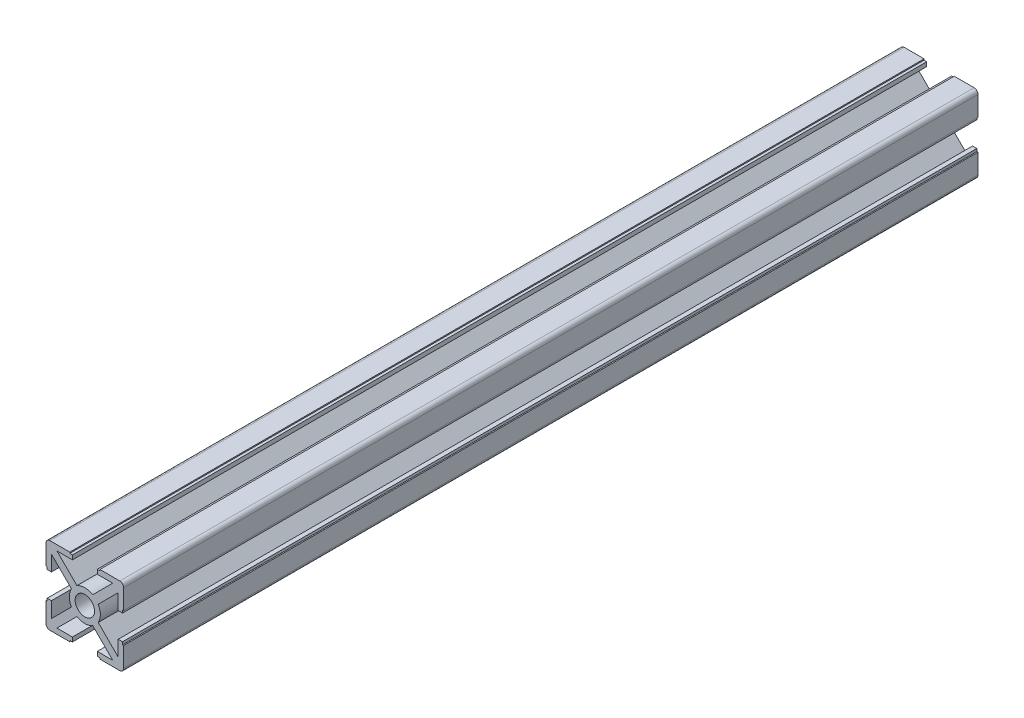
SolidWorks part; units mm, degrees
material "1060 Alloy"
ref_plane "Ön Düzlem" through (0, 0, 0) normal (0, 0, 1) x (1, 0, 0)
ref_plane "Üst Düzlem" through (0, 0, 0) normal (0, 1, 0) x (1, 0, 0)
ref_plane "Sağ Düzlem" through (0, 0, 0) normal (1, 0, 0) x (0, 0, -1)
sketch "Sketch1" plane through (0, 0, 0) normal (0, 0, 1) x (1, 0, 0)
  line L0 (-9.7071, -3.2) -> (-8.6, -3.2)
  line L2 (-10, -3.8775) -> (-10, -9)
  line L3 (-9, -10) -> (-3.8775, -10)
  line L5 (-10, -3.8775) -> (-9.7071, -3.8775)
  line L6 (-10, -10) -> (-9.7071, -9.7071) construction
  line L9 (-3.2, -8.6) -> (-7.1858, -8.6)
  line L10 (-8.6, -3.2) -> (-8.6, -7.1858)
  line L13 (-7.1858, -8.6) -> (-2.0315, -3.4457)
  line L14 (-8.6, -7.1858) -> (-3.4457, -2.0315)
  line L15 (-10.7071, -9.2929) -> (9.2929, 10.7071) construction
  line L16 (-9.2929, -10.7071) -> (10.7071, 9.2929) construction
  line L18 (-10, -10) -> (10, 10) construction
  line L19 (-2.5, 0) -> (-9.7071, 0) construction
  line L20 (0, -2.5) -> (0, -6.9362) construction
  line L21 (-3.2, -8.6) -> (-3.2, -9.7071)
  line L23 (-9.7071, -3.8775) -> (-9.7071, -3.2)
  line L24 (-3.2, -9.7071) -> (-3.8775, -9.7071)
  line L25 (-3.8775, -9.7071) -> (-3.8775, -10)
  line L28 (10, -10) -> (9.7071, -9.7071) construction
  line L30 (3.8775, -9.7071) -> (3.8775, -10)
  line L31 (3.2, -9.7071) -> (3.8775, -9.7071)
  line L32 (9.7071, -3.8775) -> (9.7071, -3.2)
  line L33 (3.2, -8.6) -> (3.2, -9.7071)
  line L34 (8.6, -7.1858) -> (3.4457, -2.0315)
  line L35 (7.1858, -8.6) -> (2.0315, -3.4457)
  line L36 (8.6, -3.2) -> (8.6, -7.1858)
  line L37 (3.2, -8.6) -> (7.1858, -8.6)
  line L38 (10, -3.8775) -> (9.7071, -3.8775)
  line L39 (9, -10) -> (3.8775, -10)
  line L40 (10, -3.8775) -> (10, -9)
  line L41 (9.7071, -3.2) -> (8.6, -3.2)
  line L42 (10, 10) -> (9.7071, 9.7071) construction
  line L43 (0, 2.5) -> (0, 6.9362) construction
  line L44 (-10, 10) -> (-9.7071, 9.7071) construction
  line L45 (9.7071, 3.2) -> (8.6, 3.2)
  line L46 (10, 3.8775) -> (10, 9)
  line L47 (9, 10) -> (3.8775, 10)
  line L48 (10, 3.8775) -> (9.7071, 3.8775)
  line L49 (3.2, 8.6) -> (7.1858, 8.6)
  line L50 (8.6, 3.2) -> (8.6, 7.1858)
  line L51 (7.1858, 8.6) -> (2.0315, 3.4457)
  line L52 (8.6, 7.1858) -> (3.4457, 2.0315)
  line L53 (3.2, 8.6) -> (3.2, 9.7071)
  line L54 (9.7071, 3.8775) -> (9.7071, 3.2)
  line L55 (3.2, 9.7071) -> (3.8775, 9.7071)
  line L56 (3.8775, 9.7071) -> (3.8775, 10)
  line L57 (-3.8775, 9.7071) -> (-3.8775, 10)
  line L58 (-3.2, 9.7071) -> (-3.8775, 9.7071)
  line L59 (-9.7071, 3.8775) -> (-9.7071, 3.2)
  line L60 (-3.2, 8.6) -> (-3.2, 9.7071)
  line L61 (-8.6, 7.1858) -> (-3.4457, 2.0315)
  line L62 (-7.1858, 8.6) -> (-2.0315, 3.4457)
  line L63 (-8.6, 3.2) -> (-8.6, 7.1858)
  line L64 (-3.2, 8.6) -> (-7.1858, 8.6)
  line L65 (-10, 3.8775) -> (-9.7071, 3.8775)
  line L66 (-9, 10) -> (-3.8775, 10)
  line L67 (-10, 3.8775) -> (-10, 9)
  line L68 (-9.7071, 3.2) -> (-8.6, 3.2)
  arc A2 (-10, -9) -> (-9, -10) centre (-9, -9) ccw
  arc A3 (-2.0315, -3.4457) -> (2.0315, -3.4457) centre (0, 0) ccw
  arc A4 (-3.4457, 2.0315) -> (-3.4457, -2.0315) centre (0, 0) ccw
  circle A5 centre (0, 0) radius 2.5
  arc A6 (3.4457, 2.0315) -> (3.4457, -2.0315) centre (0, 0) cw
  arc A7 (10, -9) -> (9, -10) centre (9, -9) cw
  arc A8 (10, 9) -> (9, 10) centre (9, 9) ccw
  arc A9 (-2.0315, 3.4457) -> (2.0315, 3.4457) centre (0, 0) cw
  arc A10 (-10, 9) -> (-9, 10) centre (-9, 9) cw
  dimension "D10" = 1
  dimension "D5" = 1.4
  dimension "D6" = 1.4
  dimension "D7" = 3.2
  dimension "D11" = 3.2
  dimension "D8" = 1
  dimension "D9" = 1
extrude "Boss-Extrude1" add sketch "Sketch1" along normal blind 220
